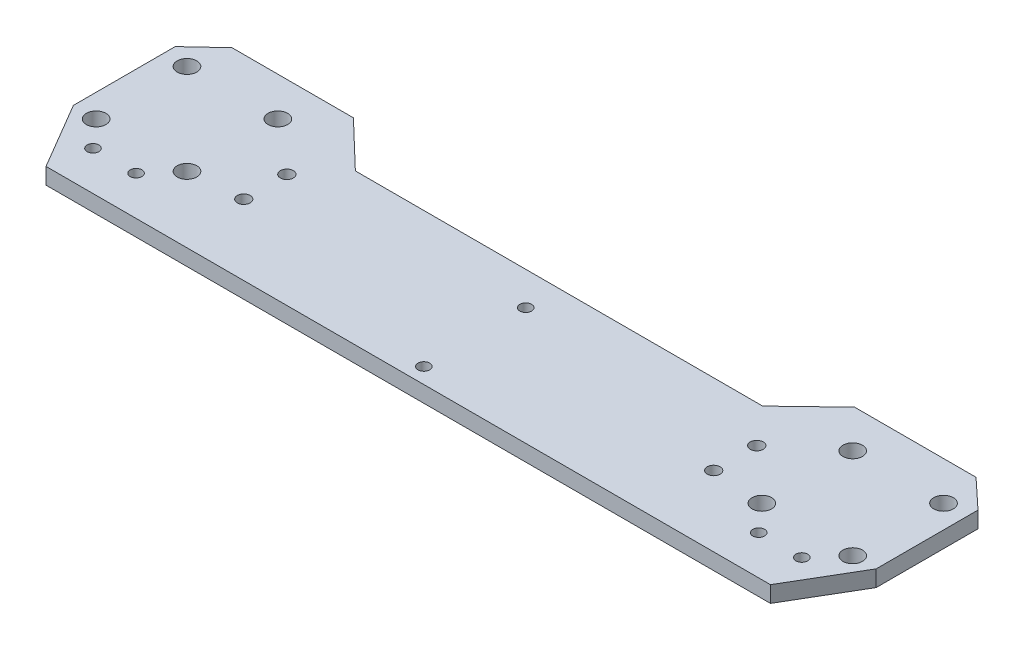
SolidWorks part; units mm, degrees
ref_plane "Front Plane" through (0, 0, 0) normal (0, 0, 1) x (1, 0, 0)
ref_plane "Top Plane" through (0, 0, 0) normal (0, 1, 0) x (1, 0, 0)
ref_plane "Right Plane" through (0, 0, 0) normal (1, 0, 0) x (0, 0, -1)
ref_plane "Plane1" through (0, -205, 0) normal (0, 1, 0) x (1, 0, 0)
sketch "Sketch1" plane through (0, -205, 0) normal (0, 1, 0) x (1, 0, 0)
  line L0 (0, 38.5) -> (0, 0) construction
  line L1 (52, 38.5) -> (64, 50)
  line L2 (64, 50) -> (95, 50)
  line L3 (95, 50) -> (102.5, 43)
  line L4 (102.5, 43) -> (102.5, 17)
  line L5 (102.5, 17) -> (92.5, 0)
  line L540 (-95, 50) -> (-102.5, 43)
  line L541 (-102.5, 43) -> (-102.5, 17)
  line L542 (-102.5, 17) -> (-92.5, 0)
  line L543 (-92.5, 0) -> (92.5, 0)
  line L549 (52, 38.5) -> (-52, 38.5)
  line L550 (-52, 38.5) -> (-64, 50)
  line L551 (-64, 50) -> (-95, 50)
  circle A0 centre (-96.6, 40.1) radius 2.5
  circle A1 centre (-73.4, 40.1) radius 2.5
  circle A2 centre (-96.6, 16.9) radius 2.5
  circle A3 centre (-73.4, 16.9) radius 2.5
  circle A4 centre (-90.5, 10) radius 1.5
  circle A5 centre (-79.5, 10) radius 1.5
  circle A6 centre (-60, 29) radius 1.65
  circle A7 centre (-60, 18) radius 1.65
  circle A8 centre (0, 30) radius 1.5
  circle A9 centre (0, 4) radius 1.5
  circle A10 centre (73.4, 40.1) radius 2.5
  circle A11 centre (60, 29) radius 1.65
  circle A12 centre (60, 18) radius 1.65
  circle A13 centre (73.4, 16.9) radius 2.5
  circle A14 centre (79.5, 10) radius 1.5
  circle A15 centre (90.5, 10) radius 1.5
  circle A16 centre (96.6, 16.9) radius 2.5
  circle A17 centre (96.6, 40.1) radius 2.5
  point P20 (0, 38.5)
  dimension "D1" = 5
  dimension "D4" = 5
  dimension "D7" = 5
  dimension "D10" = 5
  dimension "D11" = 3
  dimension "D14" = 3
  dimension "D16" = 3.3
  dimension "D17" = 3.3
  dimension "D21" = 3
  dimension "D22" = 3
  dimension "D2" = 5.9
  dimension "D3" = 9.9
  dimension "D5" = 9.9
  dimension "D6" = 23.2
  dimension "D8" = 5.9
  dimension "D9" = 23.2
  dimension "D12" = 10
  dimension "D13" = 12
  dimension "D15" = 11
  dimension "D18" = 9.5
  dimension "D19" = 42.5
  dimension "D20" = 11
  dimension "D23" = 8.5
  dimension "D24" = 26
  dimension "D25" = 185
  dimension "D26" = 104
  dimension "D27" = 10
  dimension "D28" = 17
  dimension "D29" = 26
  dimension "D30" = 7
  dimension "D31" = 7.5
  dimension "D32" = 31
  dimension "D33" = 11.5
extrude "Boss-Extrude1" add sketch "Sketch1" against normal blind 4.15
